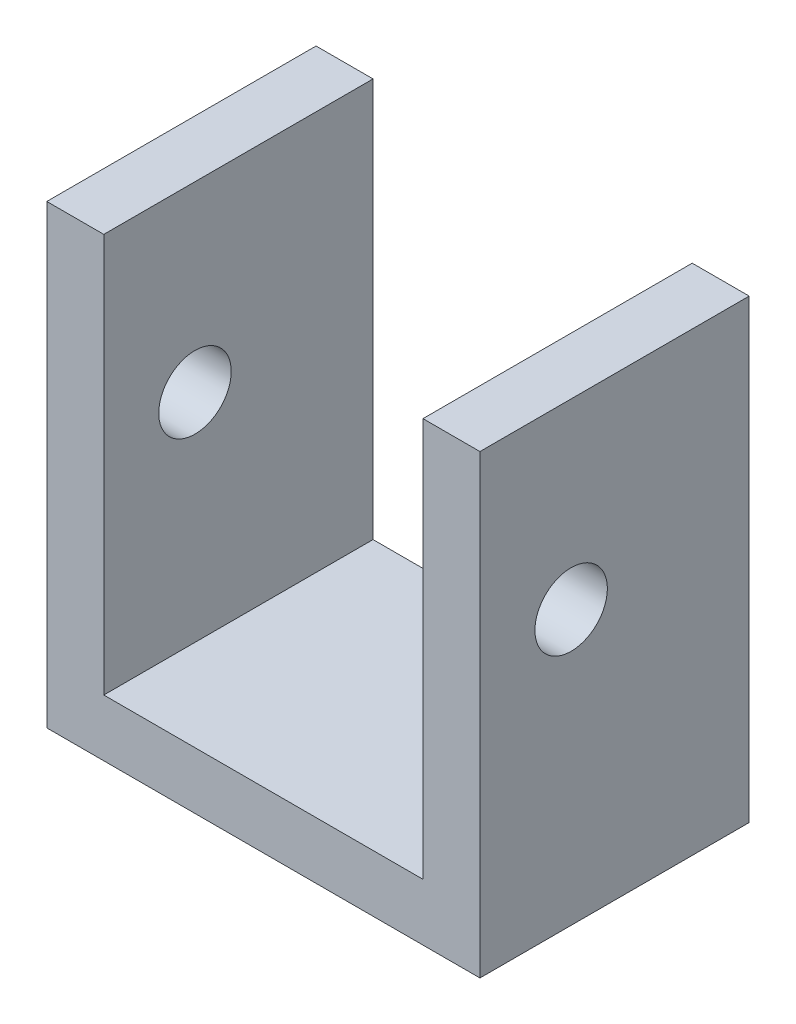
SolidWorks part; units mm, degrees
ref_plane "Front Plane" through (0, 0, 0) normal (0, 0, 1) x (1, 0, 0)
ref_plane "Top Plane" through (0, 0, 0) normal (0, 1, 0) x (1, 0, 0)
ref_plane "Right Plane" through (0, 0, 0) normal (1, 0, 0) x (0, 0, -1)
sketch "Sketch1" plane through (0, 0, 0) normal (0, 0, 1) x (1, 0, 0)
  line L1 (-12.065, 25.4) -> (12.065, 25.4)
  line L2 (-12.065, 25.4) -> (-12.065, 0)
  line L3 (-12.065, 0) -> (12.065, 0)
  line L4 (12.065, 25.4) -> (12.065, 0)
  line L5 (-8.89, 25.4) -> (8.89, 25.4)
  line L6 (-8.89, 25.4) -> (-8.89, 3.175)
  line L7 (-8.89, 3.175) -> (8.89, 3.175)
  line L8 (8.89, 25.4) -> (8.89, 3.175)
  point P4 (0, 0)
  point P9 (0, 3.175)
  point P11 (8.89, 17.2955)
  point P13 (12.065, 25.518)
  dimension "D1" = 17.78
  dimension "D2" = 24.13
  dimension "D3" = 25.4
  dimension "D4" = 3.175
extrude "Boss-Extrude1" add sketch "Sketch1" along normal blind 15 contours L1 L8 L7 L6 L2 L3 L4
sketch "Sketch2" plane through (0, 0, 0) normal (1, 0, 0) x (0, 0, -1)
  line L0 (-15, 25.4) -> (-15, 0) construction
  line L1 (-15, 0) -> (0, 0) construction
  point P0 (-9.92, 15.24)
  point P5 (-10, 9.5)
  dimension "D1" = 5.08
  dimension "D2" = 15.24
hole_wizard "#10-32 Tapped Hole1" positions "Sketch3" profile "Sketch4" tap size "#10-32" standard "ANSI Inch" end condition through all
sketch "Sketch3" plane through (12.065, 0, 0) normal (1, 0, 0) x (0, 0, -1)
  point P0 (-9.92, 15.24)
sketch "Sketch4" plane through (12.065, 15.24, 9.92) normal (0, 1, 0) x (0, 0, -1)
  line L0 (0, 0) -> (0, 24.13)
  line L1 (0, 24.13) -> (2.0193, 24.13)
  line L2 (2.0193, 24.13) -> (2.0193, 0)
  line L5 (2.0193, 0) -> (0, 0)
  line L11 (0, -6.35) -> (0, 107.95) construction
  dimension "Thru Tap Drill Dia." = 4.0386
  dimension "Thru Tap Drill Depth" = 24.13
cosmetic thread "Hole Thread1" parameters "D2"=4.826
